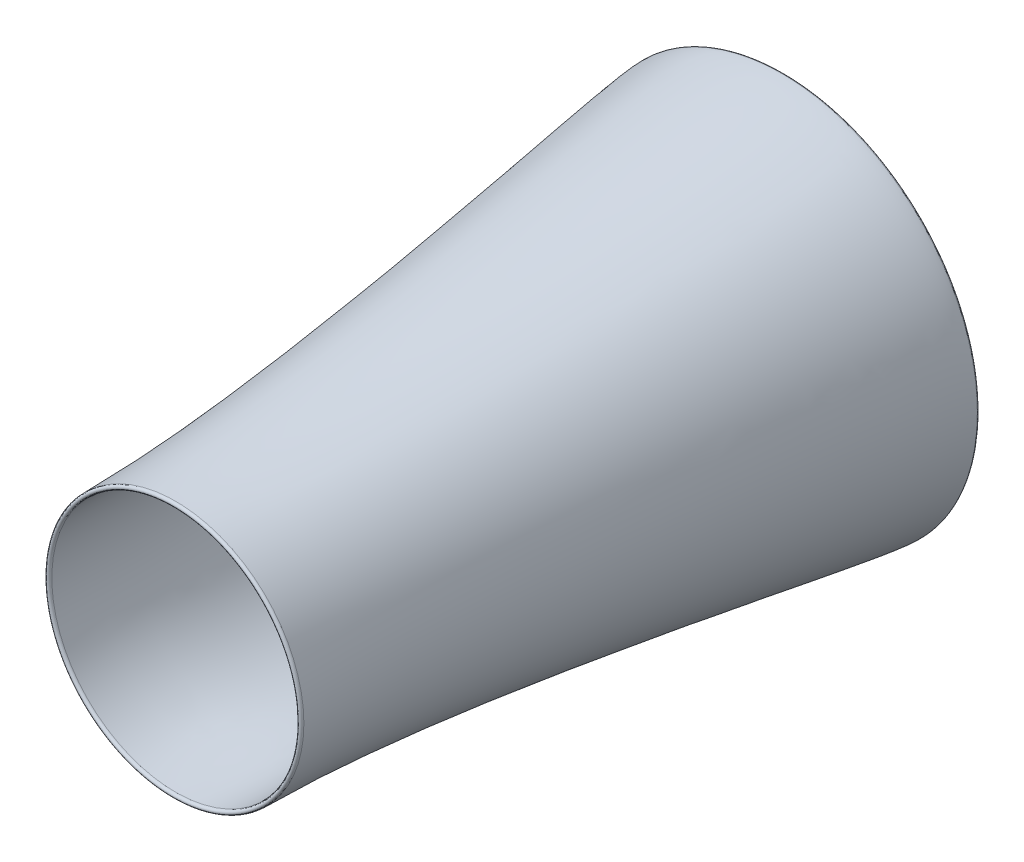
SolidWorks part; units mm, degrees
ref_plane "Front Plane" through (0, 0, 0) normal (0, 0, 1) x (1, 0, 0)
ref_plane "Top Plane" through (0, 0, 0) normal (0, 1, 0) x (1, 0, 0)
ref_plane "Right Plane" through (0, 0, 0) normal (1, 0, 0) x (0, 0, -1)
sketch "Sketch1" plane through (0, 0, 0) normal (0, 0, 1) x (1, 0, 0)
  circle A0 centre (0, 0) radius 50.8
  dimension "D1" = 101.6
ref_plane "Plane1" through (0, -254, 0) normal (0, 1, 0) x (1, 0, 0)
sketch "Sketch6" plane through (0, 0, 0) normal (0, 1, 0) x (1, 0, 0)
  line L0 (0, -99.6848) -> (0, 145.6048) construction
ref_plane "Plane2" through (0, -114.3, 0) normal (0, 1, 0) x (1, 0, 0)
sketch "Sketch12" plane through (0, 0, 0) normal (0, 1, 0) x (1, 0, 0)
  line L0 (0, -1104.7568) -> (0, -908.6135) construction
ref_plane "Plane3" through (0, 0, 203.2) normal (0, 0, 1) x (1, 0, 0)
ref_plane "Plane4" through (0, 0, 889) normal (0, 0, 1) x (1, 0, 0)
sketch "Sketch17" plane through (0, 0, 0) normal (0, 1, 0) x (1, 0, 0)
  line L0 (-259.4955, -43.5301) -> (-259.4955, 70.1436) construction
  line L1 (-110.6437, -1316.1124) -> (-110.6437, -853.5386) construction
  line L2 (-259.4955, 45.4622) -> (-387.328, 45.4622)
  line L3 (-387.328, 45.4622) -> (-387.328, -1084.8928)
  line L4 (-387.328, -1084.8928) -> (-110.6437, -1084.8928)
  spline S0 degree 3 poles (-259.4955, 45.4622) (-259.4955, -7.1736) (-207.7477, -105.8122) (-173.3147, -383.1384) (-92.4228, -818.9689) (-110.6437, -795.7842) (-110.6437, -1084.8928) knots 0 0 0 0 0.158009 0.206507 0.484977 1 1 1 1
sketch "Sketch21" plane through (0, 0, 0) normal (0, 1, 0) x (1, 0, 0)
  line L0 (-686.2823, -22.8536) -> (-686.2823, 113.778) construction
  line L1 (-450.1433, -1315.9117) -> (-450.1433, -853.874) construction
  line L2 (-603.4631, -20.0975) -> (-686.2823, -20.0975) construction
  line L3 (-434.4023, -2147.3046) -> (-450.1433, -2147.3046) construction
  line L4 (-434.4023, -2147.3046) -> (-450.1433, -2147.3046)
  line L6 (-603.4631, -20.0975) -> (-686.2823, -20.0975)
  spline S0 degree 3 poles (-603.4631, -20.0975) (-603.4631, -72.7333) (-549.077, -603.0123) (-515.7557, -762.8882) (-399.896, -1827.4671) (-434.4023, -1858.196) (-434.4023, -2147.3046) knots 0 0 0 0 0.158009 0.206507 0.484977 1 1 1 1
  spline S1 degree 3 poles (-686.2823, -20.0975) (-686.2823, -145.4815) (-450.1433, -1416.9955) (-450.1433, -2147.3046) knots 0 0 0 0 1 1 1 1
  point P10 (0, 0)
  point P11 (-434.4023, -2147.3046)
  point P12 (-450.1433, -1408.6025)
  point P13 (-538.4862, -650.1754)
  point P14 (-686.2823, -20.0975)
revolve "Revolve2" add sketch "Sketch21" angle 360 about L0
sketch "Sketch22" plane through (0, 0, 0) normal (0, 1, 0) x (1, 0, 0)
  line L0 (-686.2823, -20.0975) -> (-603.4631, -20.0975)
  line L1 (-603.4631, -23.9066) -> (-603.4631, -16.2885) construction
  line L2 (-686.2823, -18.7048) -> (-686.2823, -21.4903) construction
  spline S0 degree 3 poles (-686.2823, -20.0975) (-686.2823, -3.1642) (-603.4631, -3.1642) (-603.4631, -20.0975) knots 0 0 0 0 1 1 1 1
revolve "Revolve3" add sketch "Sketch22" angle 360 about L0
sketch "Sketch23" plane through (0, 0, 0) normal (0, 1, 0) x (1, 0, 0)
  line L0 (-450.1433, -2147.3046) -> (-434.4023, -2147.3046)
  line L1 (-450.1433, -2156.5157) -> (-450.1433, -2138.0935) construction
  line L2 (-434.4023, -2136.7316) -> (-434.4023, -2157.8776) construction
  spline S0 degree 3 poles (-450.1433, -2147.3046) (-450.1433, -2160.0046) (-434.4023, -2160.0046) (-434.4023, -2147.3046) knots 0 0 0 0 1 1 1 1
revolve "Revolve4" add sketch "Sketch23" angle 360 about L0
ref_plane "Plane5" through (289.9098, 0, 0) normal (1, 0, 0) x (0, 0, -1)
sketch "Sketch24" plane through (289.9098, 0, 0) normal (1, 0, 0) x (0, 0, -1)
  line L0 (-1123.5724, -17.6357) -> (119.2276, -17.6357) construction
  line L1 (-2147.3046, 0) -> (-20.0975, 0) construction
  line L2 (-2147.3046, -450.1433) -> (-2147.3046, 450.1433) construction
  line L3 (-20.0975, 686.2823) -> (-20.0975, -686.2823) construction
  text T0 "MD-130 Gas Turbine Engine" font "TI-Nspire" height in points 160
